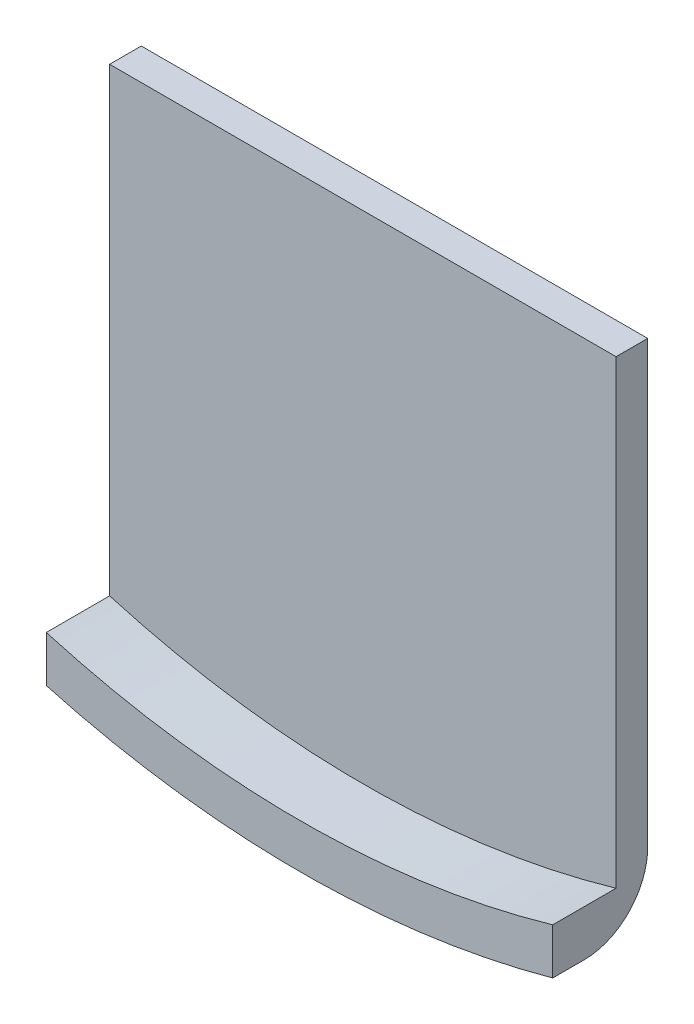
SolidWorks part; units mm, degrees
ref_plane "Front Plane" through (0, 0, 0) normal (0, 0, 1) x (1, 0, 0)
ref_plane "Top Plane" through (0, 0, 0) normal (0, 1, 0) x (1, 0, 0)
ref_plane "Right Plane" through (0, 0, 0) normal (1, 0, 0) x (0, 0, -1)
sketch "Sketch2" plane through (0, 0, 0) normal (0, 0, 1) x (1, 0, 0)
  line L0 (-40, -144.5683) -> (-40, -64.5683)
  line L1 (-40, -64.5683) -> (40, -64.5683)
  line L2 (40, -64.5683) -> (40, -144.5683)
  arc A0 (-40, -144.5683) -> (40, -144.5683) centre (0, 0) ccw
  dimension "D1" = 300
  dimension "D2" = 80
  dimension "D3" = 80
extrude "Boss-Extrude1" add sketch "Sketch2" along normal blind 15
sketch "Sketch3" plane through (0, 0, 15) normal (0, 0, 1) x (1, 0, 0)
  line L0 (-40, -137.2917) -> (-40, -64.5683)
  line L1 (-40, -64.5683) -> (-40, -144.5683) construction
  line L2 (-40, -64.5683) -> (40, -64.5683)
  line L3 (40, -64.5683) -> (40, -137.2917)
  line L4 (40, -144.5683) -> (40, -64.5683) construction
  arc A0 (-40, -137.2917) -> (40, -137.2917) centre (0, 0) ccw
  dimension "D1" = 286
extrude "Cut-Extrude1" cut sketch "Sketch3" against normal blind 10
fillet "Fillet1" radius 10 1 edges at (0, -150, 0)
